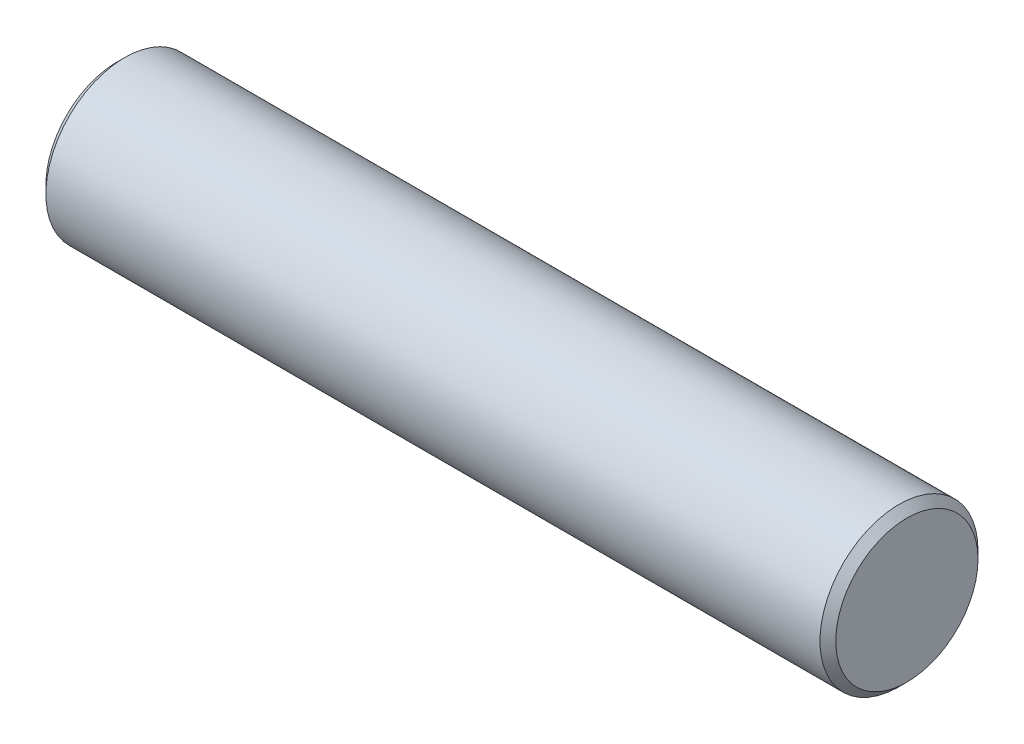
SolidWorks part; units mm, degrees
ref_plane "Спереди" through (0, 0, 0) normal (0, 0, 1) x (1, 0, 0)
ref_plane "Сверху" through (0, 0, 0) normal (0, 1, 0) x (1, 0, 0)
ref_plane "Справа" through (0, 0, 0) normal (1, 0, 0) x (0, 0, -1)
other "Configuration Table"
sketch "Эскиз1" plane through (0, 0, 0) normal (1, 0, 0) x (0, 0, -1)
  circle A0 centre (0, 0) radius 10
  dimension "D1" = 20
extrude "Бобышка-Вытянуть1" add sketch "Эскиз1" along normal blind 100 contours A0
chamfer "Фаска1" distance 1 angle 45 2 edges at (0, 0, -10) (100, 0, -10)
